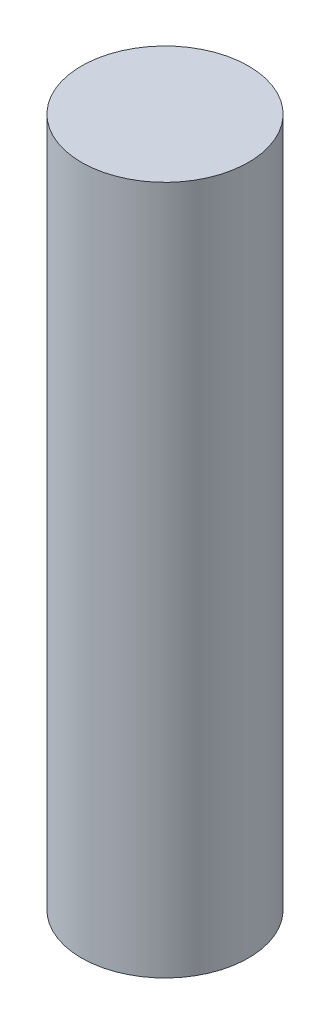
SolidWorks part; units mm, degrees
ref_plane "Front Plane" through (0, 0, 0) normal (0, 0, 1) x (1, 0, 0)
ref_plane "Top Plane" through (0, 0, 0) normal (0, 1, 0) x (1, 0, 0)
ref_plane "Right Plane" through (0, 0, 0) normal (1, 0, 0) x (0, 0, -1)
sketch "Sketch1" plane through (0, 0, 0) normal (0, 1, 0) x (1, 0, 0)
  circle A0 centre (-35.4005, 11.8469) radius 2.4
extrude "Boss-Extrude1" add sketch "Sketch1" along normal blind 19.8
